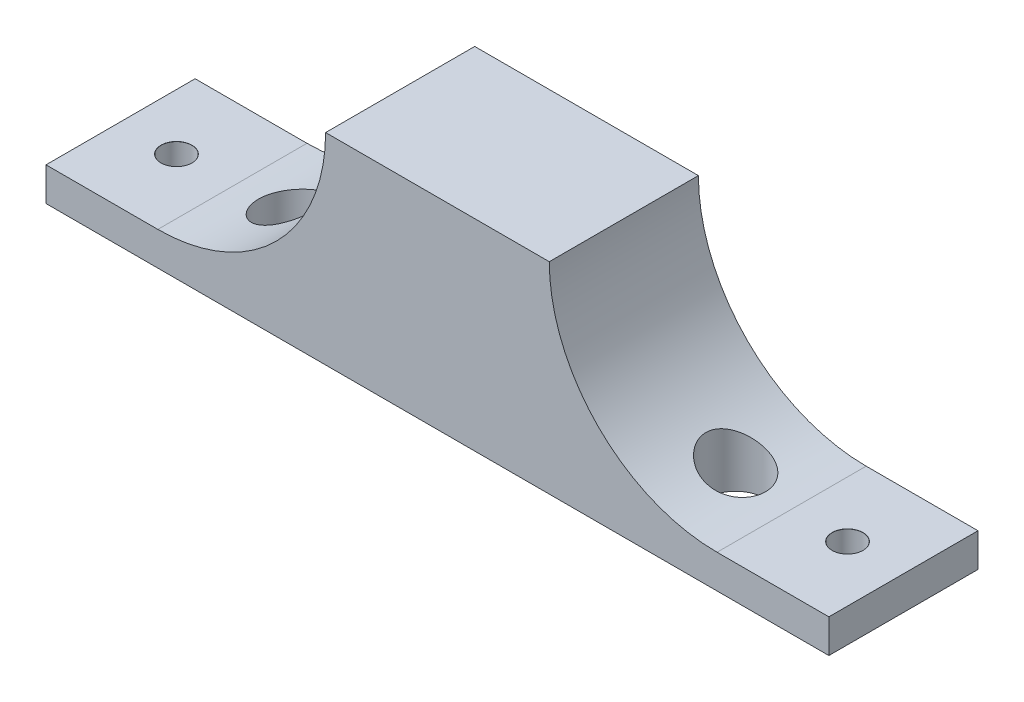
SolidWorks part; units mm, degrees
ref_plane "Front Plane" through (0, 0, 0) normal (0, 0, 1) x (1, 0, 0)
ref_plane "Top Plane" through (0, 0, 0) normal (0, 1, 0) x (1, 0, 0)
ref_plane "Right Plane" through (0, 0, 0) normal (1, 0, 0) x (0, 0, -1)
sketch "Sketch1" plane through (0, 0, 0) normal (0, 1, 0) x (1, 0, 0)
  line L1 (-60, 0) -> (0, 0)
  line L2 (-60, 0) -> (-60, -40)
  line L3 (-60, -40) -> (0, -40)
  line L4 (0, 0) -> (0, -40)
  dimension "D1" = 60
  dimension "D2" = 40
  dimension "D3" = 0
  dimension "D4" = 0
extrude "Boss-Extrude1" add sketch "Sketch1" along normal blind 54
sketch "Sketch2" plane through (0, 54, 0) normal (0, 1, 0) x (1, 0, 0)
  line L1 (-51.25, 11.25) -> (-8.75, 11.25)
  line L2 (-51.25, 11.25) -> (-51.25, -31.25)
  line L3 (-51.25, -31.25) -> (-8.75, -31.25)
  line L4 (-8.75, 11.25) -> (-8.75, -31.25)
  line L5 (-60, 0) -> (-60, -40) construction
  line L7 (-60, -40) -> (0, -40) construction
  line L9 (-43, -31.25) -> (-17, -31.25)
  line L10 (-43, -31.25) -> (-43, -40)
  line L11 (-43, -40) -> (-17, -40)
  line L12 (-17, -31.25) -> (-17, -40)
  point P4 (-51.25, -10)
  dimension "D1" = 42.5
  dimension "D2" = 42.5
  dimension "D3" = 8.75
  dimension "D4" = 8.75
  dimension "D5" = 26
  dimension "D6" = 0
  dimension "D7" = 8.25
  dimension "D8" = 0
sketch "Sketch3" plane through (0, 0, 0) normal (0, 1, 0) x (1, 0, 0)
  line L0 (0, -40) -> (0, 0) construction
  line L1 (0, 0) -> (75, 0)
  line L2 (0, 0) -> (0, -40)
  line L3 (0, -40) -> (75, -40)
  line L4 (75, 0) -> (75, -40)
  line L5 (0, 0) -> (-60, 0) construction
  circle A0 centre (30, -20) radius 8
  dimension "D5" = 20
  dimension "D7" = 16
  dimension "D1" = 0
  dimension "D2" = 0
  dimension "D3" = 40
  dimension "D4" = 75
  dimension "D6" = 45
extrude "Boss-Extrude2" add sketch "Sketch3" along normal blind 54
sketch "Sketch4" plane through (0, 0, 40) normal (0, 0, 1) x (1, 0, 0)
  line L0 (-60, 54) -> (75, 54) construction
  line L1 (75, 54) -> (75, 0) construction
  line L3 (45, 54) -> (75, 54)
  line L4 (45, 54) -> (45, 9)
  line L5 (45, 9) -> (75, 9)
  line L6 (75, 54) -> (75, 9)
  circle A0 centre (45, 54) radius 45
  line M7 (75, 0) -> (75, 54)
  line M8 (75, 54) -> (-60, 54)
  dimension "D3" = 90
  dimension "D1" = 0
  dimension "D2" = 30
  dimension "D4" = 0
  dimension "D5" = 30
  dimension "D6" = 0
  dimension "D7" = 45
extrude "Cut-Extrude2" cut sketch "Sketch4" against normal blind 60 contours A0 L5 M7 | A0 L4 M8 | L4 A0 L6 M8
ref_plane "Plane4" through (-30, 0, 0) normal (1, 0, 0) x (0, 0, -1)
hole_wizard "Tap Drill for M8 Helicoil1" positions "Sketch6" profile "Sketch7" hole size "M8x1.0" standard "ANSI Metric" end condition through all
sketch "Sketch6" plane through (0, 9, 0) normal (0, 1, 0) x (1, 0, 0)
  line L0 (45, 0) -> (75, 0) construction
  line L2 (75, 0) -> (75, -40) construction
  point P0 (60, -20)
  dimension "D1" = 20
  dimension "D2" = 15
sketch "Sketch7" plane through (60, 9, 20) normal (1, 0, 0) x (0, 0, 1)
  line L0 (0, 0) -> (0, 9)
  line L1 (0, 9) -> (4.125, 9)
  line L2 (4.125, 9) -> (4.125, 0.025)
  line L3 (4.125, 0.025) -> (4.15, 0)
  line L5 (4.15, 0) -> (0, 0)
  line L6 (-4.125, 0.025) -> (-4.15, 0) construction
  line L11 (0, -6.35) -> (0, 107.95) construction
  dimension "Thru Hole Dia." = 8.25
  dimension "Thru Hole Depth" = 9
  dimension "Near C'Sink Dia." = 8.3
  dimension "Near C'Sink Angle" = 90
mirror "Mirror1" about plane through (-30, 0, 0) normal (1, 0, 0) of "Tap Drill for M8 Helicoil1", "Cut-Extrude2", "Boss-Extrude2"
